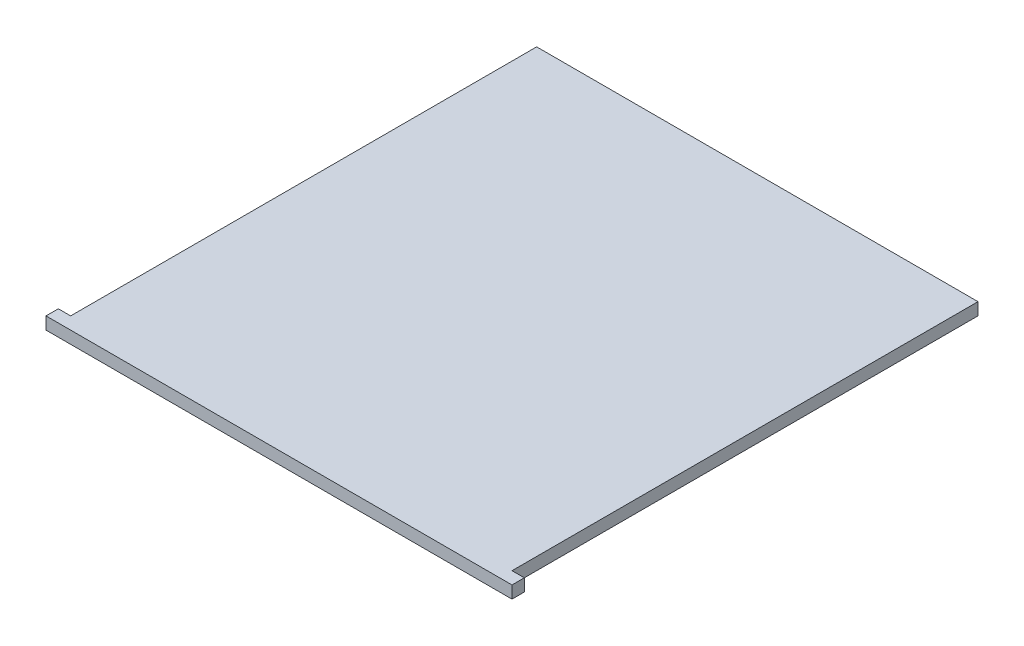
SolidWorks part; units mm, degrees
ref_plane "Front Plane" through (0, 0, 0) normal (0, 0, 1) x (1, 0, 0)
ref_plane "Top Plane" through (0, 0, 0) normal (0, 1, 0) x (1, 0, 0)
ref_plane "Right Plane" through (0, 0, 0) normal (1, 0, 0) x (0, 0, -1)
sketch "Sketch1" plane through (0, 0, 0) normal (0, 1, 0) x (1, 0, 0)
  line L1 (0, 0) -> (96.012, 0)
  line L2 (0, 0) -> (0, 98.552)
  line L3 (0, 98.552) -> (96.012, 98.552)
  line L4 (96.012, 0) -> (96.012, 98.552)
  dimension "D1" = 96.012
  dimension "D2" = 98.552
extrude "Boss-Extrude1" add sketch "Sketch1" along normal blind 2.54
sketch "Sketch2" plane through (0, 2.54, 0) normal (0, 1, 0) x (1, 0, 0)
  line L1 (0, 0) -> (96.012, 0) construction
  line L2 (0, 98.552) -> (2.54, 98.552)
  line L3 (0, 98.552) -> (0, 2.54)
  line L4 (0, 2.54) -> (2.54, 2.54)
  line L5 (2.54, 98.552) -> (2.54, 2.54)
  line L7 (96.012, 98.552) -> (93.472, 98.552)
  line L8 (96.012, 98.552) -> (96.012, 2.54)
  line L9 (96.012, 2.54) -> (93.472, 2.54)
  line L10 (93.472, 98.552) -> (93.472, 2.54)
  dimension "D1" = 2.54
  dimension "D2" = 2.54
  dimension "D3" = 2.54
  dimension "D4" = 2.54
extrude "Cut-Extrude1" cut sketch "Sketch2" against normal blind 2.54
